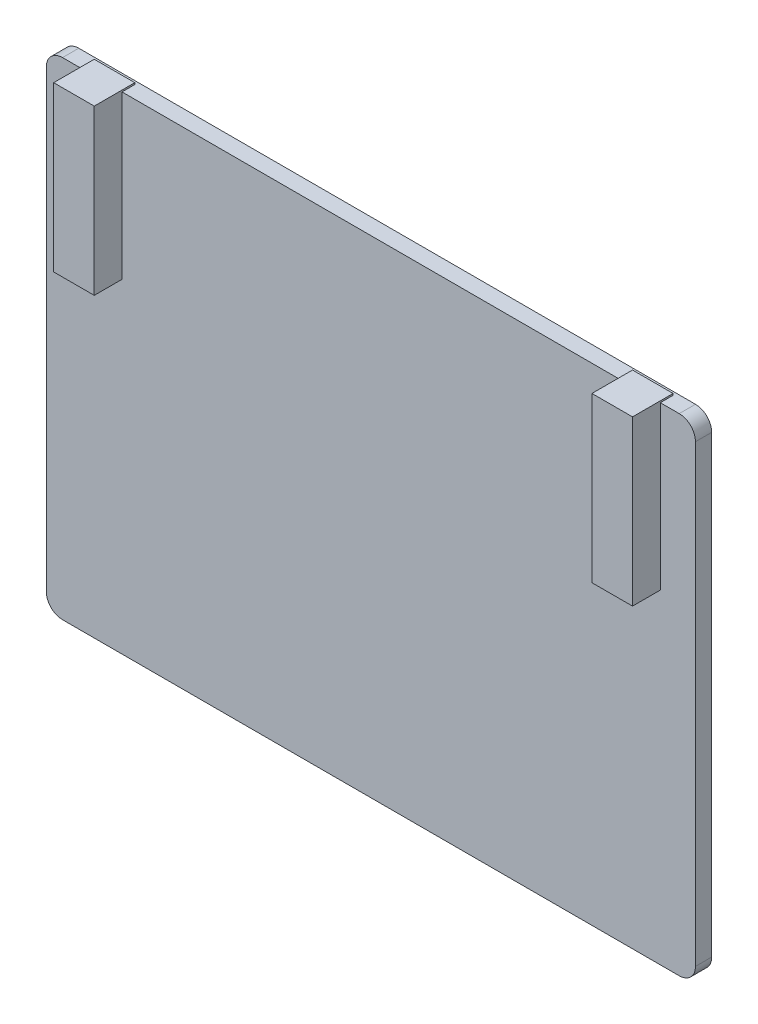
SolidWorks part; units mm, degrees
ref_plane "Front Plane" through (0, 0, 0) normal (0, 0, 1) x (1, 0, 0)
ref_plane "Top Plane" through (0, 0, 0) normal (0, 1, 0) x (1, 0, 0)
ref_plane "Right Plane" through (0, 0, 0) normal (1, 0, 0) x (0, 0, -1)
sketch "Sketch1" plane through (0, 0, 0) normal (0, 0, 1) x (1, 0, 0)
  line L3 (-50.8, -38.1) -> (50.8, -38.1)
  line L4 (-50.8, -38.1) -> (-50.8, 38.1)
  line L5 (-50.8, 38.1) -> (50.8, 38.1)
  line L6 (50.8, -38.1) -> (50.8, 38.1)
  line L7 (-50.8, -38.1) -> (50.8, 38.1) construction
  line L8 (-50.8, 38.1) -> (50.8, -38.1) construction
  point P4 (0, 0)
  dimension "D1" = 101.6
  dimension "D2" = 76.2
extrude "Boss-Extrude1" add sketch "Sketch1" along normal blind 2.54
sketch "Sketch2" plane through (0, 38.1, 0) normal (0, 1, 0) x (1, 0, 0)
  line L0 (-50.8, -1.27) -> (-30.4038, -1.27) construction
  line L1 (-50.8, -2.54) -> (-50.8, 0) construction
  line L2 (-43.4575, -2.3812) -> (-43.4575, -4.2167) construction
  line L3 (0, -1.397) -> (0, 1.397) construction
  line L4 (43.4575, -2.3812) -> (24.3667, -2.3813) construction
  line L5 (43.4575, -2.3812) -> (43.4575, -4.2167) construction
  line L6 (50.8, -1.27) -> (30.4038, -1.27) construction
  line L7 (-43.4575, -2.3812) -> (-24.3667, -2.3813) construction
  circle A0 centre (-42.124, -3.7147) radius 1.3335
  circle A1 centre (42.124, -3.7147) radius 1.3335
  circle A2 centre (-42.124, -3.7147) radius 1.5875
  circle A3 centre (42.124, -3.7147) radius 1.5875
  dimension "D4" = 2.667
  dimension "D5" = 0.254
  dimension "D6" = 0.254
  dimension "D1" = 84.248
  dimension "D2" = 1.1112
extrude "Boss-Extrude2" add sketch "Sketch2" against normal blind 25.4
sketch "Sketch3" plane through (0, 38.1, 0) normal (0, 1, 0) x (1, 0, 0)
  line L0 (0, -1.397) -> (0, 1.397) construction
  circle A1 centre (-42.124, -3.7147) radius 1.5875
  circle A2 centre (42.124, -3.7147) radius 1.5875
  dimension "D1" = 3.175
extrude "Boss-Extrude3" add sketch "Sketch3" along normal blind 0.254
fillet "Fillet1" radius 2.54 4 edges at (-50.8, -38.1, 1.27) (50.8, -38.1, 1.27) (50.8, 38.1, 1.27) (-50.8, 38.1, 1.27)
sketch "Sketch4" plane through (0, 38.354, 0) normal (0, 1, 0) x (1, 0, 0)
  line L1 (-45.299, -6.8897) -> (-38.949, -6.8897)
  line L2 (-45.299, -6.8897) -> (-45.299, -0.5397)
  line L3 (-45.299, -0.5397) -> (-38.949, -0.5397)
  line L4 (-38.949, -6.8897) -> (-38.949, -0.5397)
  line L5 (-45.299, -6.8897) -> (-38.949, -0.5397) construction
  line L6 (-45.299, -0.5397) -> (-38.949, -6.8897) construction
  line L7 (38.949, -6.8897) -> (45.299, -6.8897)
  line L8 (38.949, -6.8897) -> (38.949, -0.5397)
  line L9 (38.949, -0.5397) -> (45.299, -0.5397)
  line L10 (45.299, -6.8897) -> (45.299, -0.5397)
  line L11 (38.949, -6.8897) -> (45.299, -0.5397) construction
  line L12 (38.949, -0.5397) -> (45.299, -6.8897) construction
  point P0 (-42.124, -3.7147)
  point P6 (42.124, -3.7147)
  dimension "D1" = 6.35
  dimension "D2" = 6.35
  dimension "D3" = 6.35
  dimension "D4" = 6.35
extrude "Boss-Extrude4" add sketch "Sketch4" against normal up to surface (25.654 mm away)
sketch "Sketch5" plane through (0, 12.7, 0) normal (0, -1, 0) x (1, 0, 0)
  circle A0 centre (-42.124, 3.7147) radius 2.54
  circle A9 centre (42.124, 3.7147) radius 2.54
  dimension "D1" = 5.08
  dimension "D2" = 5.08
extrude "Cut-Extrude1" cut sketch "Sketch5" against normal blind 24.13
